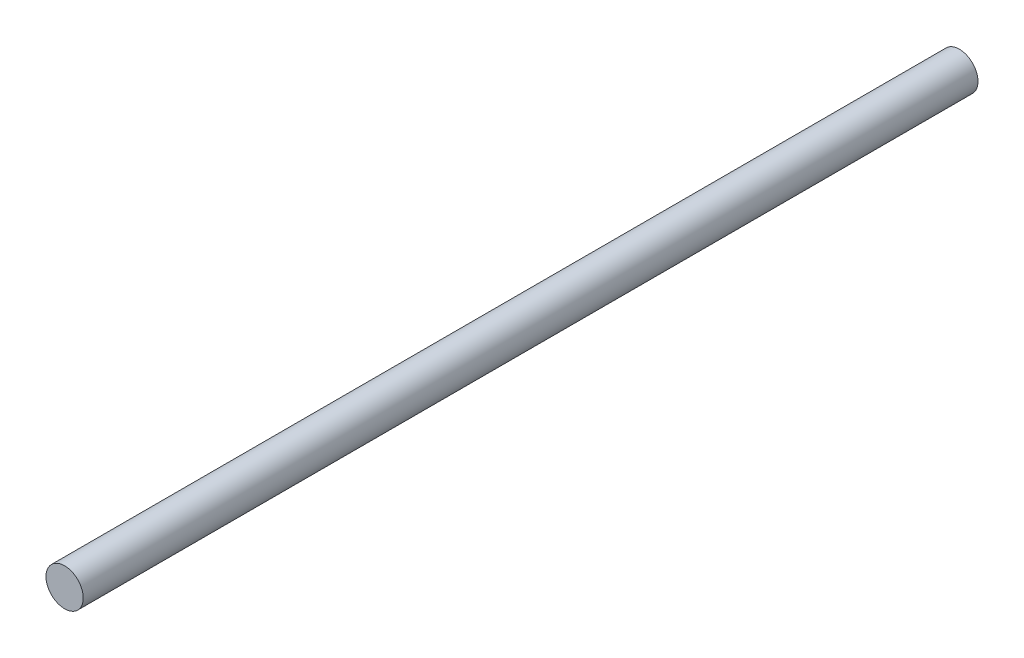
SolidWorks part; units mm, degrees
ref_plane "Front Plane" through (0, 0, 0) normal (0, 0, 1) x (1, 0, 0)
ref_plane "Top Plane" through (0, 0, 0) normal (0, 1, 0) x (1, 0, 0)
ref_plane "Right Plane" through (0, 0, 0) normal (1, 0, 0) x (0, 0, -1)
sketch "Sketch1" plane through (0, 0, 0) normal (0, 0, 1) x (1, 0, 0)
  circle A0 centre (0, 0) radius 6.35
  dimension "D1" = 12.7
extrude "Boss-Extrude1" add sketch "Sketch1" along normal blind 304.8
